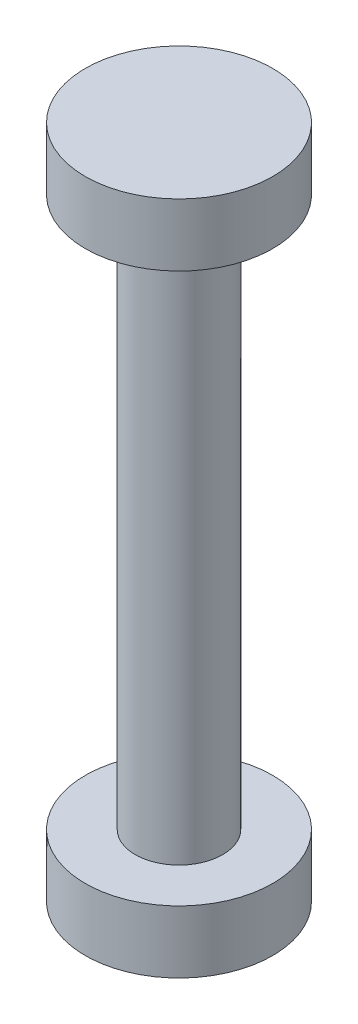
SolidWorks part; units mm, degrees
ref_plane "Front Plane" through (0, 0, 0) normal (0, 0, 1) x (1, 0, 0)
ref_plane "Top Plane" through (0, 0, 0) normal (0, 1, 0) x (1, 0, 0)
ref_plane "Right Plane" through (0, 0, 0) normal (1, 0, 0) x (0, 0, -1)
sketch "Sketch1" plane through (0, 0, 0) normal (0, 1, 0) x (1, 0, 0)
  line L0 (0, 18.8268) -> (0, -19.4528) construction
  line L1 (-54.1996, 0) -> (61.7124, 0) construction
  circle A0 centre (0, 0) radius 15
  dimension "D1" = 30
extrude "Boss-Extrude1" add sketch "Sketch1" against normal blind 10
sketch "Sketch2" plane through (0, -10, 0) normal (0, -1, 0) x (1, 0, 0)
  circle A0 centre (0, 0) radius 7
  dimension "D1" = 14
extrude "Boss-Extrude2" add sketch "Sketch2" along normal blind 98
sketch "Sketch4" plane through (0, -108, 0) normal (0, -1, 0) x (1, 0, 0)
  circle A0 centre (0, 0) radius 15
  dimension "D1" = 30
extrude "Boss-Extrude3" add sketch "Sketch4" against normal blind 10
